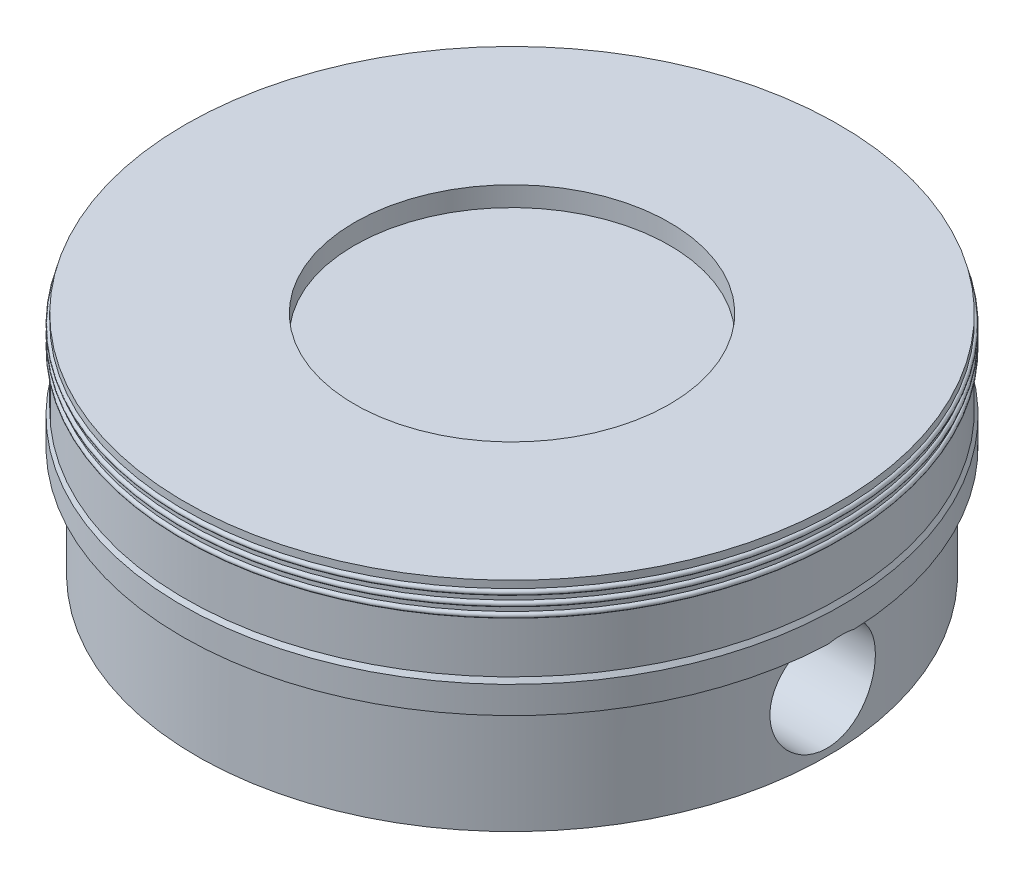
SolidWorks part; units mm, degrees
ref_plane "Front Plane" through (0, 0, 0) normal (0, 0, 1) x (1, 0, 0)
ref_plane "Top Plane" through (0, 0, 0) normal (0, 1, 0) x (1, 0, 0)
ref_plane "Right Plane" through (0, 0, 0) normal (1, 0, 0) x (0, 0, -1)
sketch "Sketch1" plane through (0, 0, 0) normal (0, 0, 1) x (1, 0, 0)
  line L0 (0, 3) -> (0, 0) construction
  line L1 (0, 0) -> (5, 0) construction
  line L2 (4.78, 0) -> (3.43, 0)
  line L3 (3.43, 0) -> (3.43, 1.93)
  line L4 (3.43, 1.93) -> (4.2, 1.93)
  line L5 (4.2, 1.93) -> (4.2, 2.33)
  line L6 (4.2, 2.33) -> (0, 2.33)
  line L7 (0, 2.33) -> (0, 3.13)
  line L8 (0, 3.13) -> (2.39, 3.13)
  line L9 (2.39, 3.13) -> (2.39, 3.43)
  line L10 (2.39, 3.43) -> (4.96, 3.43)
  line L11 (4.96, 3.43) -> (4.96, 2.16)
  line L12 (4.96, 2.16) -> (5, 2.09)
  line L13 (5, 2.09) -> (5, 1.68)
  line L14 (5, 1.68) -> (4.78, 1.68)
  line L15 (4.78, 1.68) -> (4.78, 0)
  arc A0 (4.96, 3.24) -> (4.96, 3.32) centre (4.96, 3.28) ccw
  arc A1 (4.96, 3.09) -> (4.96, 3.17) centre (4.96, 3.13) ccw
  arc A2 (4.96, 2.94) -> (4.96, 3.02) centre (4.96, 2.98) ccw
  point P21 (0, 2.93)
  point P22 (0, 0)
  point P23 (0, 0)
  point P26 (0, 0)
  point P31 (-0.0254, 3.1643)
  point P32 (0, 0)
  point P33 (0.0068, 3.2073)
  point P34 (0.0337, 3.13)
  point P35 (0, 0)
  point P36 (0, 0)
  dimension "D18" = 0.08
  dimension "D1" = 5
  dimension "D2" = 3
  dimension "D3" = 4.96
  dimension "D4" = 0.04
  dimension "D5" = 5
  dimension "D6" = 0.22
  dimension "D7" = 1.68
  dimension "D8" = 1.35
  dimension "D9" = 1.93
  dimension "D10" = 0.4
  dimension "D11" = 2.57
  dimension "D12" = 0.3
  dimension "D13" = 0.8
  dimension "D14" = 4.2
  dimension "D15" = 0.15
  dimension "D16" = 0.15
  dimension "D17" = 0.15
  dimension "D19" = 0.41
  dimension "D20" = 0.07
revolve "Revolve1" add sketch "Sketch1" angle 360 about L0
sketch "Sketch3" plane through (0, 0, 0) normal (0, -1, 0) x (1, 0, 0)
  line L0 (0, 3.43) -> (0, 0) construction
  line L1 (0, 0) -> (-3.43, 0) construction
  line L2 (-1.75, 2.95) -> (-1.75, -2.95)
  line L3 (1.75, 2.95) -> (1.75, -2.95)
  circle A0 centre (0, 0) radius 3.43 construction
  arc A1 (-1.75, 2.95) -> (-1.75, -2.95) centre (0, 0) ccw
  arc A2 (1.75, -2.95) -> (1.75, 2.95) centre (0, 0) ccw
  dimension "D1" = 3.5
extrude "Boss-Extrude2" add sketch "Sketch3" against normal up to next contours L2 A1 | L3 A2
sketch "Sketch4" plane through (0, 0, 0) normal (1, 0, 0) x (0, 0, -1)
  circle A0 centre (0, 0.9065) radius 0.8
  dimension "D1" = 1.6
  dimension "D2" = 0.9065
extrude "Cut-Extrude1" cut sketch "Sketch4" against normal through all both and the other way through all
